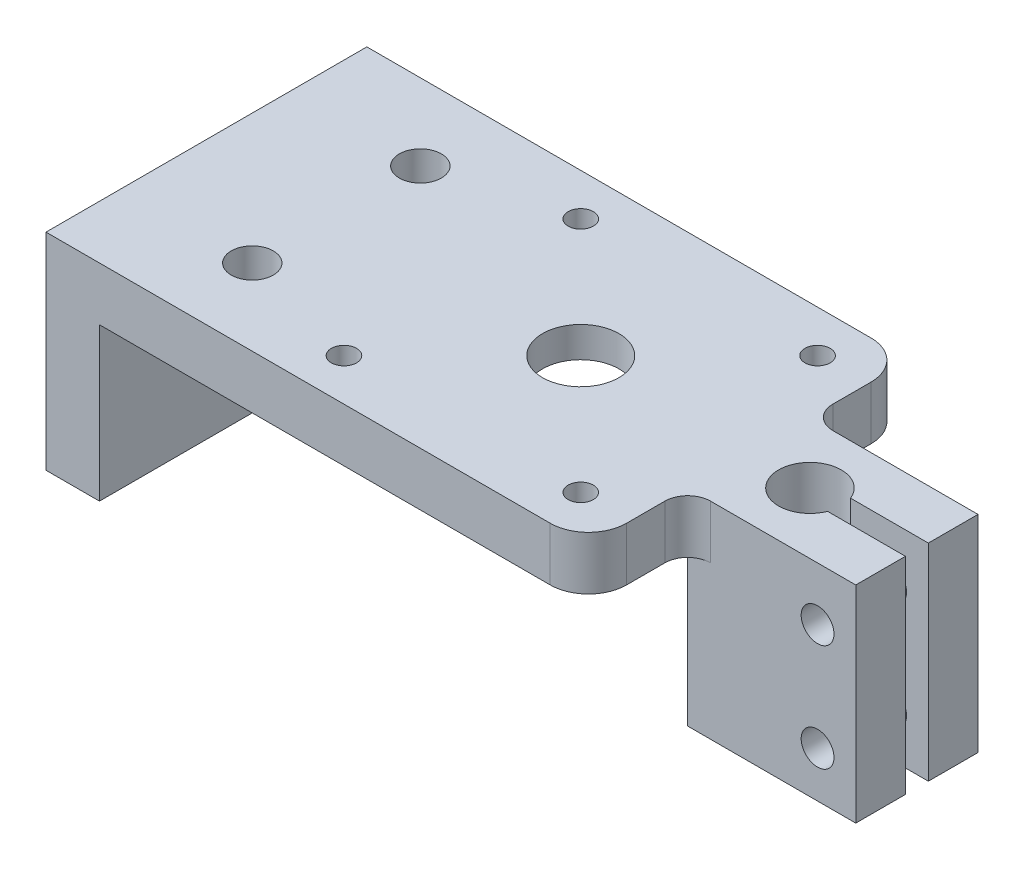
SolidWorks part; units mm, degrees
material "ABS PC"
ref_plane "Front Plane" through (0, 0, 0) normal (0, 0, 1) x (1, 0, 0)
ref_plane "Top Plane" through (0, 0, 0) normal (0, 1, 0) x (1, 0, 0)
ref_plane "Right Plane" through (0, 0, 0) normal (1, 0, 0) x (0, 0, -1)
sketch "Sketch1" plane through (0, 0, 0) normal (0, 1, 0) x (1, 0, 0)
  line L1 (-32, -21) -> (32, -21)
  line L2 (-32, -21) -> (-32, 21)
  line L3 (-32, 21) -> (32, 21)
  line L4 (32, -21) -> (32, 21)
  line L5 (-32, -21) -> (32, 21) construction
  line L6 (-32, 21) -> (32, -21) construction
  point P0 (0, 0)
  dimension "D1" = 64
  dimension "D2" = 42
extrude "Boss-Extrude1" add sketch "Sketch1" along normal blind 7 contours L3 L4 L1 L2
sketch "Sketch11" plane through (0, 0, 0) normal (0, 1, 0) x (1, 0, 0)
  line L0 (32, -8) -> (32, 8)
  line L1 (32, -8) -> (54, -8)
  line L2 (32, 8) -> (54, 8)
  line L3 (54, -8) -> (54, 8)
  line L4 (32, -21) -> (32, 21) construction
  line L5 (54, 0) -> (32, 0) construction
  dimension "D1" = 22
  dimension "D2" = 16
extrude "Boss-Extrude3" add sketch "Sketch11" along normal blind 7 and the other way blind 20
sketch "Sketch3" plane through (0, 0, 0) normal (0, 1, 0) x (1, 0, 0)
  circle A0 centre (10, 0) radius 12
  dimension "D1" = 24
extrude "Cut-Extrude2" cut sketch "Sketch3" along normal blind 3
sketch "Sketch2" plane through (0, 7, 0) normal (0, 1, 0) x (1, 0, 0)
  circle A0 centre (40, 0) radius 4.1
  dimension "D1" = 8.2
  dimension "D2" = 40
extrude "Cut-Extrude1" cut sketch "Sketch2" against normal through all
sketch "Sketch4" plane through (0, 7, 0) normal (0, 1, 0) x (1, 0, 0)
  line L0 (-32, -21) -> (-32, 21) construction
  line L1 (-32, 21) -> (32, 21) construction
  line L2 (-32, -21) -> (32, -21) construction
  circle A0 centre (-22, 11) radius 2.75
  circle A1 centre (-22, -11) radius 2.75
  dimension "D1" = 5.5
  dimension "D4" = 5.5
  dimension "D2" = 10
  dimension "D3" = 10
  dimension "D5" = 10
  dimension "D6" = 10
extrude "Cut-Extrude3" cut sketch "Sketch4" against normal through all
sketch "Sketch7" plane through (0, 7, 0) normal (0, 1, 0) x (1, 0, 0)
  circle A0 centre (-5.5, 15.5) radius 1.65
  circle A1 centre (25.5, 15.5) radius 1.65
  circle A2 centre (25.5, -15.5) radius 1.65
  circle A3 centre (-5.5, -15.5) radius 1.65
  dimension "D1" = 3.3
  dimension "D2" = 3.3
  dimension "D3" = 3.3
  dimension "D4" = 3.3
extrude "Cut-Extrude5" cut sketch "Sketch7" against normal through all
sketch "Sketch8" plane through (-32, 0, 0) normal (-1, 0, 0) x (0, 0, 1)
  line L1 (-21, 7) -> (21, 7)
  line L2 (-21, 7) -> (-21, -20)
  line L3 (-21, -20) -> (21, -20)
  line L4 (21, 7) -> (21, -20)
  line L5 (21, 7) -> (21, 0) construction
  dimension "D1" = 27
extrude "Boss-Extrude2" add sketch "Sketch8" along normal blind 7
sketch "Sketch9" plane through (-39, 0, 0) normal (-1, 0, 0) x (0, 0, 1)
  line L0 (-21, -20) -> (21, -20) construction
  line L1 (0, 7) -> (0, -20) construction
  line L2 (21, 7) -> (-21, 7) construction
  circle A0 centre (0, -10) radius 2.7
  dimension "D2" = 5.4
  dimension "D1" = 10
extrude "Cut-Extrude6" cut sketch "Sketch9" against normal blind 13 and the other way through all
sketch "Sketch10" plane through (0, 7, 0) normal (0, 1, 0) x (1, 0, 0)
  circle A0 centre (10, 0) radius 5
  dimension "D1" = 10
extrude "Cut-Extrude7" cut sketch "Sketch10" against normal blind 20
sketch "Sketch15" plane through (0, 0, -8) normal (0, 0, -1) x (-1, 0, 0)
  line L0 (-54, -20) -> (-54, 7) construction
  line L1 (-54, 7) -> (-32, 7) construction
  circle A0 centre (-49, 0) radius 2.15
  circle A1 centre (-49, -14) radius 2.15
  dimension "D1" = 4.3
  dimension "D2" = 5
  dimension "D3" = 7
  dimension "D4" = 14
extrude "Cut-Extrude8" cut sketch "Sketch15" against normal blind 22
sketch "Sketch16" plane through (0, 7, 0) normal (0, 1, 0) x (1, 0, 0)
  line L0 (54, -8) -> (54, 8) construction
  line L1 (40, -1.5) -> (54, -1.5)
  line L2 (40, -1.5) -> (40, 1.5)
  line L3 (40, 1.5) -> (54, 1.5)
  line L4 (54, -1.5) -> (54, 1.5)
  line L5 (40, 0) -> (54, 0) construction
  dimension "D1" = 14
  dimension "D2" = 3
extrude "Cut-Extrude9" cut sketch "Sketch16" against normal through all
fillet "Fillet1" radius 3 2 edges at (32, 3.5, 8) (32, 3.5, -8)
fillet "Fillet2" radius 5 2 edges at (32, 3.5, -21) (32, 3.5, 21)
